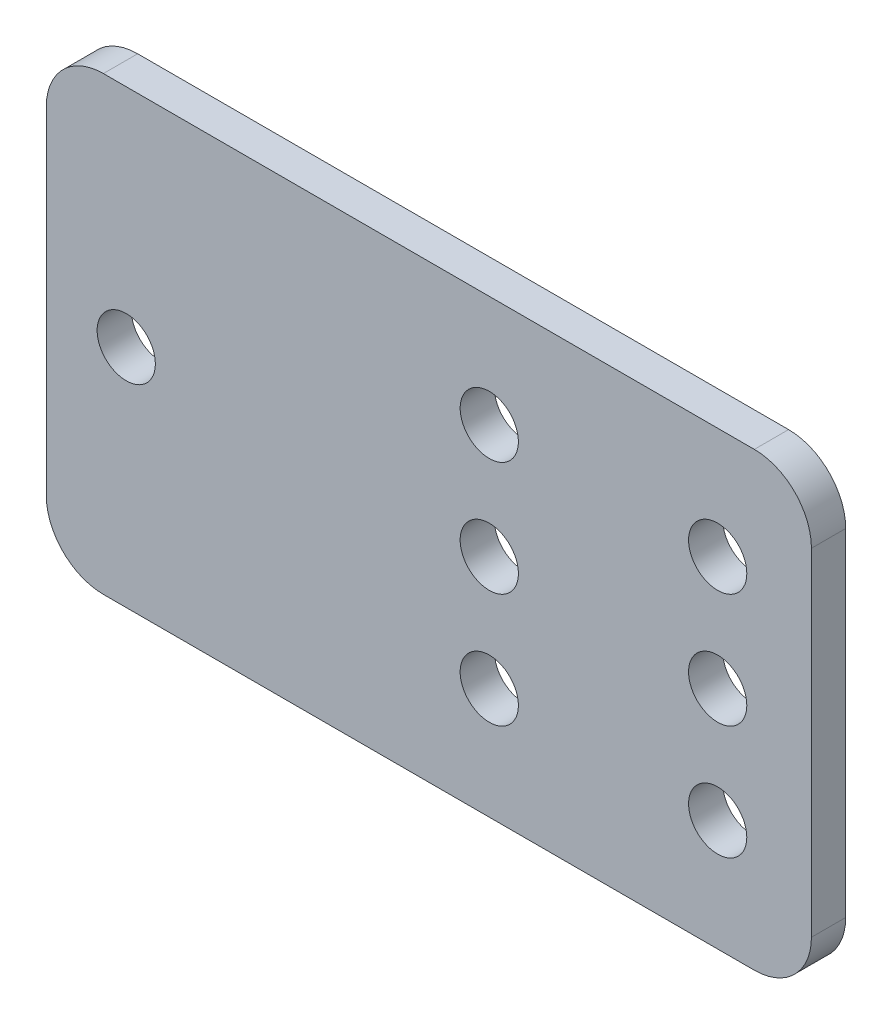
SolidWorks part; units mm, degrees
ref_plane "Front Plane" through (0, 0, 0) normal (0, 0, 1) x (1, 0, 0)
ref_plane "Top Plane" through (0, 0, 0) normal (0, 1, 0) x (1, 0, 0)
ref_plane "Right Plane" through (0, 0, 0) normal (1, 0, 0) x (0, 0, -1)
sketch "Sketch1" plane through (0, 0, 0) normal (0, 0, 1) x (1, 0, 0)
  line L0 (0, 0) -> (5.29, 0) construction
  line L1 (-28.5, -19.75) -> (28.5, -19.75)
  line L2 (-33.5, -14.75) -> (-33.5, 14.75)
  line L3 (-28.5, 19.75) -> (28.5, 19.75)
  line L4 (33.5, -14.75) -> (33.5, 14.75)
  line L5 (-33.5, -19.75) -> (33.5, 19.75) construction
  line L6 (-33.5, 19.75) -> (33.5, -19.75) construction
  line L7 (5.29, 0) -> (5.29, 10) construction
  circle A0 centre (5.29, 10) radius 2.55
  circle A1 centre (25.29, 10) radius 2.55
  circle A2 centre (5.29, 0) radius 2.55
  circle A3 centre (25.29, 0) radius 2.55
  circle A4 centre (5.29, -10) radius 2.55
  circle A5 centre (25.29, -10) radius 2.55
  circle A6 centre (-26.5, 0) radius 2.55
  arc A7 (-28.5, -19.75) -> (-33.5, -14.75) centre (-28.5, -14.75) cw
  arc A8 (28.5, -19.75) -> (33.5, -14.75) centre (28.5, -14.75) ccw
  arc A9 (28.5, 19.75) -> (33.5, 14.75) centre (28.5, 14.75) cw
  arc A10 (-33.5, 14.75) -> (-28.5, 19.75) centre (-28.5, 14.75) cw
  point P0 (0, 0)
  dimension "D5" = 5.1
  dimension "D7" = 5.1
  dimension "D9" = 5
  dimension "D1" = 67
  dimension "D2" = 39.5
  dimension "D3" = 10
  dimension "D4" = 38.79
  dimension "D6" = 20
  dimension "D8" = 7
extrude "Boss-Extrude1" add sketch "Sketch1" along normal mid plane 3
